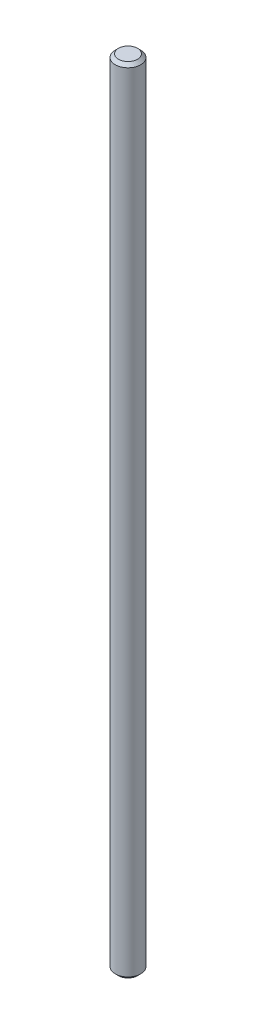
SolidWorks part; units mm, degrees
ref_plane "前视基准面" through (0, 0, 0) normal (0, 0, 1) x (1, 0, 0)
ref_plane "上视基准面" through (0, 0, 0) normal (0, 1, 0) x (1, 0, 0)
ref_plane "右视基准面" through (0, 0, 0) normal (1, 0, 0) x (0, 0, -1)
sketch "草图1" plane through (0, 0, 0) normal (0, 1, 0) x (1, 0, 0)
  circle A0 centre (0, 0) radius 4
  dimension "D1" = 8
extrude "凸台-拉伸1" add sketch "草图1" along normal blind 250
chamfer "倒角1" distance 1 angle 45 2 edges at (0, 0, 4) (0, 250, 4)
